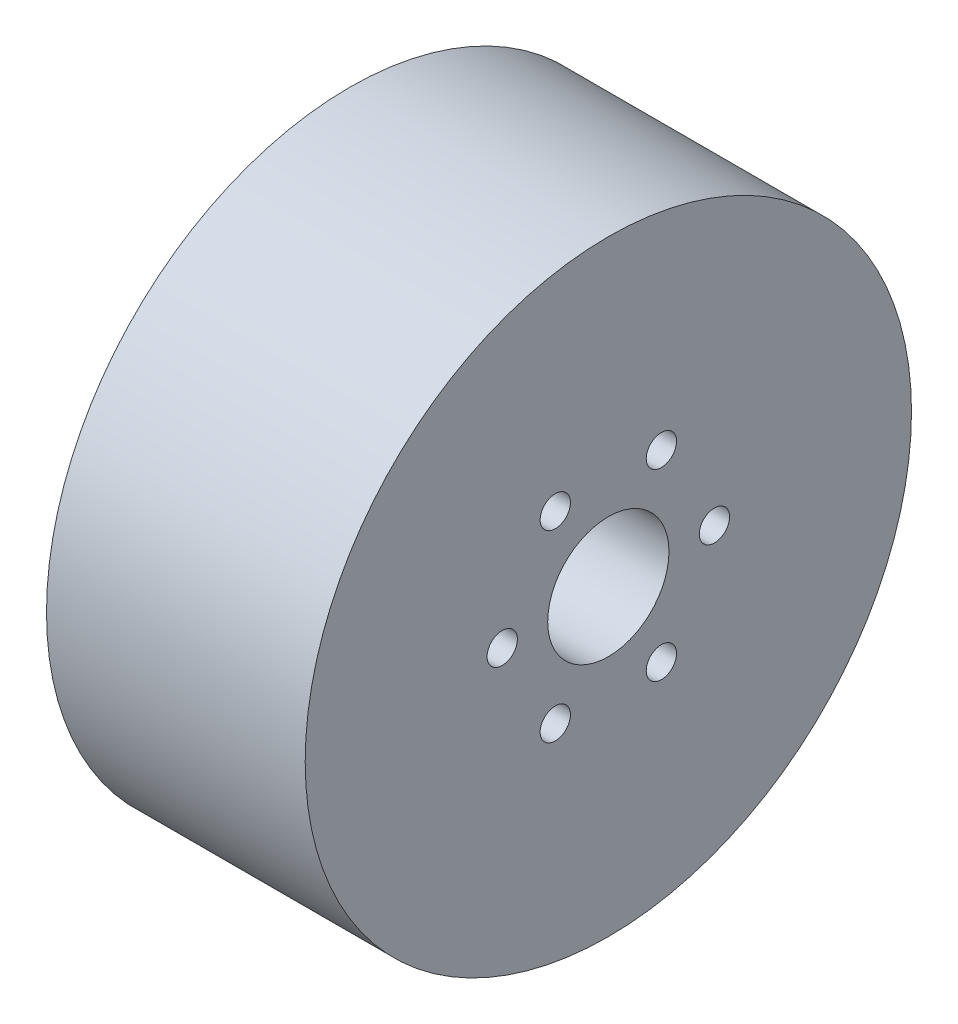
SolidWorks part; units mm, degrees
material "ｼﾘｺﾝ ｺﾞﾑ"
ref_plane "正面" through (0, 0, 0) normal (0, 0, 1) x (1, 0, 0)
ref_plane "平面" through (0, 0, 0) normal (0, 1, 0) x (1, 0, 0)
ref_plane "右側面" through (0, 0, 0) normal (1, 0, 0) x (0, 0, -1)
sketch "ｽｹｯﾁ1" plane through (0, 0, 0) normal (1, 0, 0) x (0, 0, -1)
  circle A0 centre (0, 0) radius 30
  dimension "D1" = 60
extrude "ﾎﾞｽ - 押し出し1" add sketch "ｽｹｯﾁ1" along normal blind 25.6 contours A0
sketch "ｽｹｯﾁ2" plane through (0, 0, 0) normal (-1, 0, 0) x (0, 0, 1)
  circle A0 centre (0, 0) radius 6
  circle A1 centre (10.5, 0) radius 1.5
  circle A2 centre (5.25, -9.0933) radius 1.5
  circle A3 centre (-5.25, -9.0933) radius 1.5
  circle A4 centre (-10.5, 0) radius 1.5
  circle A5 centre (-5.25, 9.0933) radius 1.5
  circle A6 centre (5.25, 9.0933) radius 1.5
  point P18 (0, 0)
  dimension "D1" = 12
  dimension "D2" = 3
  dimension "D3" = 6
extrude "ｶｯﾄ - 押し出し1" cut sketch "ｽｹｯﾁ2" against normal blind 30
